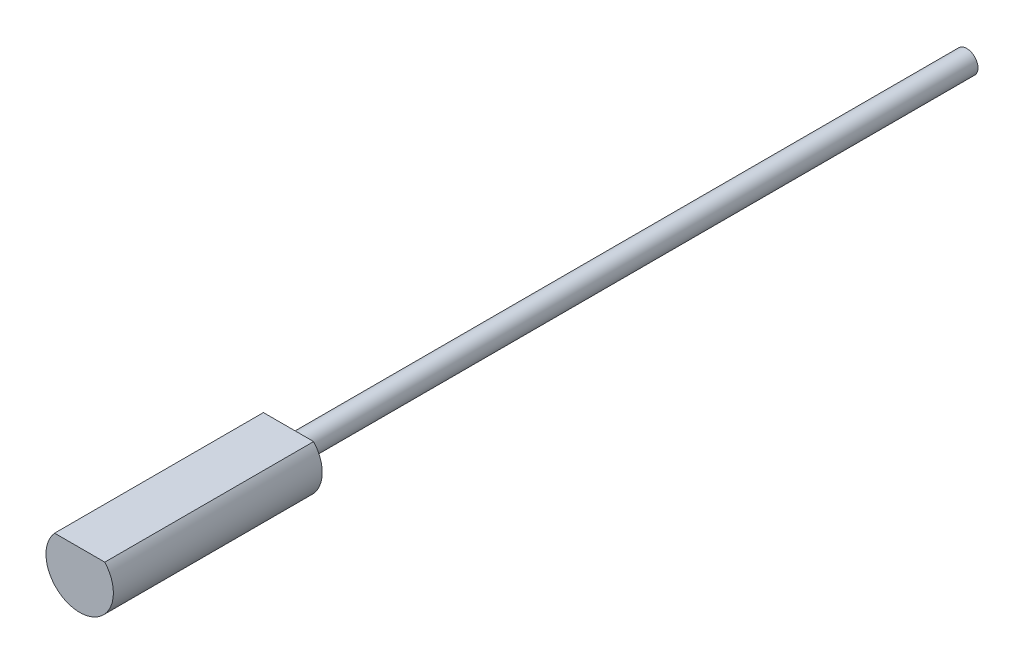
SolidWorks part; units mm, degrees
ref_plane "Front Plane" through (0, 0, 0) normal (0, 0, 1) x (1, 0, 0)
ref_plane "Top Plane" through (0, 0, 0) normal (0, 1, 0) x (1, 0, 0)
ref_plane "Right Plane" through (0, 0, 0) normal (1, 0, 0) x (0, 0, -1)
sketch "Sketch1" plane through (0, 0, 0) normal (0, 0, 1) x (1, 0, 0)
  circle A0 centre (0, 0) radius 0.5
extrude "Boss-Extrude1" add sketch "Sketch1" along normal blind 30.2
sketch "Sketch2" plane through (0, 0, 30.2) normal (0, 0, 1) x (1, 0, 0)
  line L2 (1.118, 1) -> (-1.118, 1)
  arc A1 (-1.118, 1) -> (1.118, 1) centre (0, 0) ccw
  circle M2 centre (0, 0) radius 0.5
extrude "Boss-Extrude2" add sketch "Sketch2" along normal blind 9.3 contours L2 A1 M2 | M2
